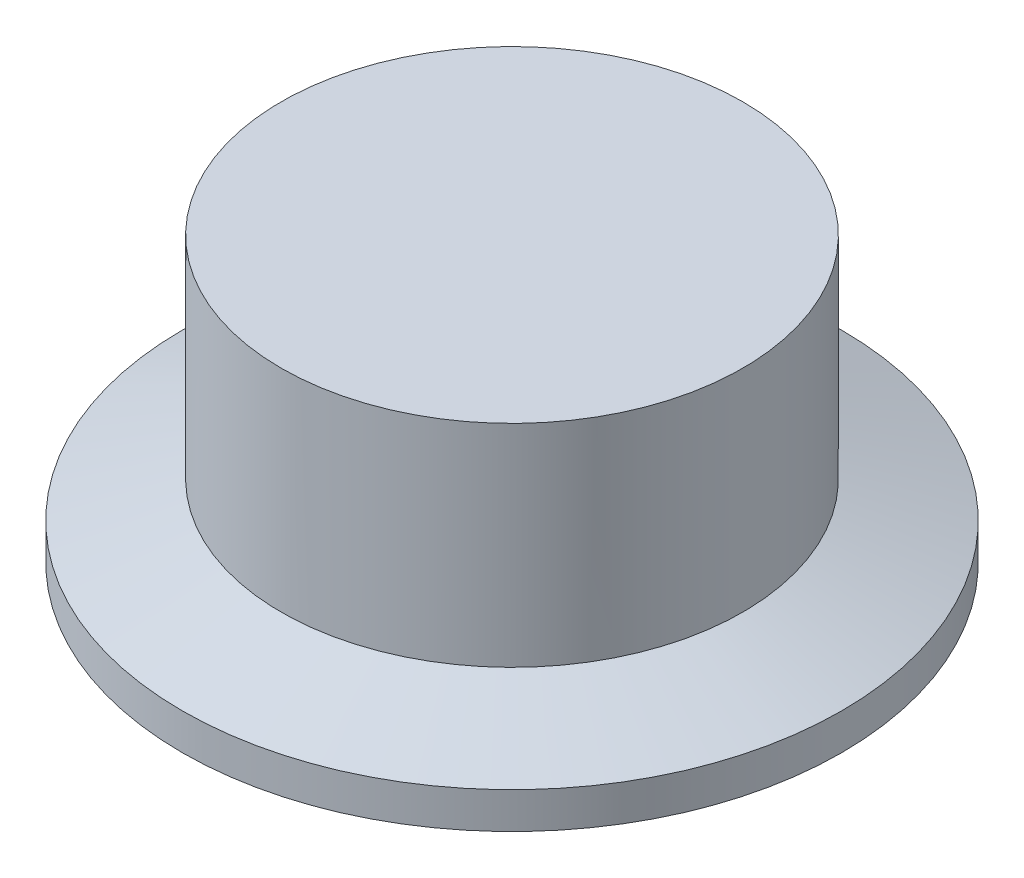
SolidWorks part; units mm, degrees
material "6061-T6 (SS)"
ref_plane "Front Plane" through (0, 0, 0) normal (0, 0, 1) x (1, 0, 0)
ref_plane "Top Plane" through (0, 0, 0) normal (0, 1, 0) x (1, 0, 0)
ref_plane "Right Plane" through (0, 0, 0) normal (1, 0, 0) x (0, 0, -1)
sketch "Sketch1" plane through (0, 0, 0) normal (0, 1, 0) x (1, 0, 0)
  circle A0 centre (0, 0) radius 93.726
  dimension "D1" = 187.452
extrude "Boss-Extrude1" add sketch "Sketch1" along normal mid plane 9.652
sketch "Sketch2" plane through (0, 0, 0) normal (0, 0, 1) x (1, 0, 0)
  line L0 (0, -18.3275) -> (0, 20.8308) construction
  line L1 (0, -4.826) -> (-25.4, -4.826)
  line L2 (-93.726, -4.826) -> (93.726, -4.826) construction
  line L3 (0, -4.826) -> (0, 1.27)
  spline S0 degree 3 poles (0, 1.27) (-5.1197, 1.5129) (-13.6852, -0.4966) (-22.1585, -2.9398) (-25.4, -4.826) knots 0 0 0 0 0.575799 1 1 1 1
  dimension "D1" = 25.4
  dimension "D2" = 6.096
revolve "Cut-Revolve1" cut sketch "Sketch2" angle 360 about L0
sketch "Sketch4" plane through (0, 4.826, 0) normal (0, 1, 0) x (1, 0, 0)
  circle A0 centre (0, 0) radius 85.09
  circle A1 centre (0, 0) radius 79.375
  dimension "D1" = 170.18
  dimension "D2" = 158.75
extrude "Boss-Extrude2" add sketch "Sketch4" along normal blind 12.7
ref_plane "Plane1" through (0, 0, -85.09) normal (0, 0, -1) x (-1, 0, 0)
sketch "Sketch5" plane through (0, 0, -85.09) normal (0, 0, -1) x (-1, 0, 0)
  line L0 (0, 19.2786) -> (0, -19.2786) construction
  line L1 (79.375, 17.526) -> (-79.375, 17.526) construction
  circle A0 centre (0, 11.176) radius 1.3525
  dimension "D1" = 2.7051
  dimension "D2" = 6.35
extrude "Cut-Extrude2" cut sketch "Sketch5" against normal blind 12.7
pattern_circular "CirPattern1" count 12 over 360 about axis through (0, 17.526, 0) along (0, -1, 0) of "Cut-Extrude2"
mirror "Mirror2" about plane through (0, 0, 0) normal (0, 1, 0) of "CirPattern1", "Cut-Extrude2", "Boss-Extrude2"
sketch "Sketch6" plane through (0, 4.826, 0) normal (0, 1, 0) x (1, 0, 0)
  line L0 (-63.5, 0) -> (-69.85, 0)
  line L1 (0, -69.85) -> (0, -63.5)
  line L2 (0, -19.2786) -> (0, 19.2786) construction
  arc A0 (-69.85, 0) -> (0, -69.85) centre (0, 0) ccw
  arc A1 (-63.5, 0) -> (0, -63.5) centre (0, 0) ccw
  dimension "D1" = 69.85
  dimension "D2" = 63.5
  dimension "D3" = 90
extrude "Cut-Extrude3" [suppressed] cut sketch "Sketch6" against normal up to surface (9.652 mm away)
sketch "Sketch7" plane through (0, 4.826, 0) normal (0, 1, 0) x (1, 0, 0)
  circle A0 centre (0, 0) radius 25.4
  circle A1 centre (0, 0) radius 127.6638
  dimension "D1" = 50.8
extrude "Cut-Extrude4" cut sketch "Sketch7" against normal through all both and the other way through all
sketch "Sketch8" plane through (0, 4.826, 0) normal (0, 1, 0) x (1, 0, 0)
  circle A0 centre (0, 0) radius 25.4
extrude "Boss-Extrude3" add sketch "Sketch8" along normal blind 5.842
sketch "Sketch9" plane through (0, 0, 0) normal (0, 0, 1) x (1, 0, 0)
  line L0 (25.4, -2.032) -> (17.78, 0.7415)
  line L1 (17.78, 0.7415) -> (17.78, 10.668)
  line L2 (17.78, 10.668) -> (25.4, 10.668)
  line L3 (25.4, 10.668) -> (25.4, -2.032)
  line L4 (25.4, 10.668) -> (-25.4, 10.668) construction
  line L5 (0, 0) -> (0, 9.2327) construction
  dimension "D1" = 17.78
  dimension "D2" = 70
  dimension "D3" = 12.7
revolve "Cut-Revolve2" cut sketch "Sketch9" angle 360 about L5
sketch "Sketch10" plane through (0, 10.668, 0) normal (0, 1, 0) x (1, 0, 0)
  circle A0 centre (0, 0) radius 17.78
extrude "Boss-Extrude4" add sketch "Sketch10" along normal blind 6.35
